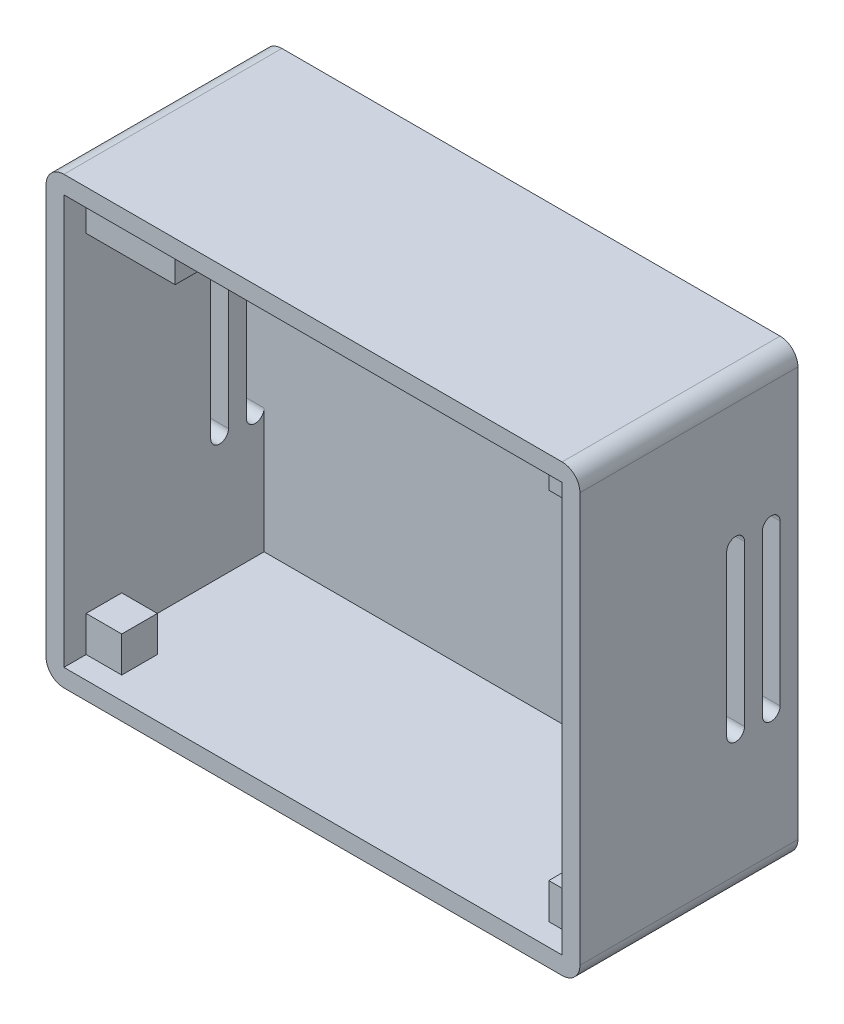
SolidWorks part; units mm, degrees
ref_plane "Спереди" through (0, 0, 0) normal (0, 0, 1) x (1, 0, 0)
ref_plane "Сверху" through (0, 0, 0) normal (0, 1, 0) x (1, 0, 0)
ref_plane "Справа" through (0, 0, 0) normal (1, 0, 0) x (0, 0, -1)
sketch "Эскиз1" plane through (0, 0, 0) normal (0, 0, 1) x (1, 0, 0)
  line L0 (-28, -25) -> (28, -25)
  line L5 (30, -23) -> (30, 23)
  line L8 (-30, 23) -> (-30, -23)
  line L9 (-28, 25) -> (28, 25)
  arc A0 (-28, 25) -> (-30, 23) centre (-28, 23) ccw
  arc A1 (28, 25) -> (30, 23) centre (28, 23) cw
  arc A2 (-30, -23) -> (-28, -25) centre (-28, -23) ccw
  arc A3 (28, -25) -> (30, -23) centre (28, -23) ccw
  point P0 (0, 0)
extrude "Бобышка-Вытянуть8" add sketch "Эскиз1" along normal blind 2 contours L9 A1 L5 A3 L0 A2 L8 A0
sketch "Эскиз6" plane through (0, 0, 2) normal (0, 0, 1) x (1, 0, 0)
  line L0 (-28, 25) -> (28, 25)
  line L1 (30, 23) -> (30, -23)
  line L2 (28, -25) -> (-28, -25)
  line L5 (-28, -23) -> (28, -23)
  line L6 (28, 23) -> (28, -23)
  line L7 (-30, -23) -> (-30, 23)
  line L8 (-18, 23) -> (28, 23)
  line L9 (-18, 23) -> (-18, 18)
  line L10 (-18, 18) -> (-28, 18)
  line L11 (-28, 18) -> (-28, -23)
  arc A0 (-28, 25) -> (-30, 23) centre (-28, 23) ccw
  arc A1 (-28, 25) -> (-30, 23) centre (-28, 23) ccw construction
  arc A2 (-28, -25) -> (-30, -23) centre (-28, -23) cw
  arc A3 (-30, -23) -> (-28, -25) centre (-28, -23) ccw construction
  arc A4 (28, -25) -> (30, -23) centre (28, -23) ccw
  arc A5 (28, -25) -> (30, -23) centre (28, -23) ccw construction
  arc A6 (28, 25) -> (30, 23) centre (28, 23) cw
  arc A7 (30, 23) -> (28, 25) centre (28, 23) ccw construction
extrude "Бобышка-Вытянуть11" add sketch "Эскиз6" along normal blind 20
sketch "Эскиз8" plane through (0, 23, 0) normal (0, -1, 0) x (1, 0, 0)
  line L1 (28, 22) -> (24, 22)
  line L2 (28, 22) -> (28, 18)
  line L3 (28, 18) -> (24, 18)
  line L4 (24, 22) -> (24, 18)
extrude "Бобышка-Вытянуть12" add sketch "Эскиз8" along normal blind 4
sketch "Эскиз9" plane through (0, -23, 0) normal (0, 1, 0) x (1, 0, 0)
  line L1 (28, -22) -> (24, -22)
  line L2 (28, -22) -> (28, -18)
  line L3 (28, -18) -> (24, -18)
  line L4 (24, -22) -> (24, -18)
  line L5 (-28, -22) -> (-24, -22)
  line L6 (-28, -22) -> (-28, -18)
  line L7 (-28, -18) -> (-24, -18)
  line L8 (-24, -22) -> (-24, -18)
extrude "Бобышка-Вытянуть13" add sketch "Эскиз9" along normal blind 4
sketch "Эскиз10" plane through (0, 0, 22) normal (0, 0, 1) x (1, 0, 0)
  line L0 (-28, 25) -> (28, 25)
  line L1 (-30, 23) -> (-30, -23)
  line L2 (-28, -25) -> (28, -25)
  line L3 (30, -23) -> (30, 23)
  line L5 (-28, 23) -> (28, 23)
  line L6 (-28, 23) -> (-28, -23)
  line L7 (-28, -23) -> (28, -23)
  line L8 (28, 23) -> (28, -23)
  arc A0 (-28, 25) -> (-30, 23) centre (-28, 23) ccw
  arc A1 (-28, 25) -> (-30, 23) centre (-28, 23) ccw construction
  arc A2 (-28, -25) -> (-30, -23) centre (-28, -23) cw
  arc A3 (28, -25) -> (30, -23) centre (28, -23) ccw
  arc A4 (28, -25) -> (30, -23) centre (28, -23) ccw construction
  arc A5 (28, 25) -> (30, 23) centre (28, 23) cw
extrude "Бобышка-Вытянуть14" add sketch "Эскиз10" along normal blind 2.5
sketch "Эскиз11" plane through (-30, 0, 0) normal (-1, 0, 0) x (0, 0, 1)
  line L0 (0, 23) -> (24.5, 23)
  point P3 (0, 0)
  point P4 (0, 0)
sketch "Эскиз15" plane through (-30, 0, 0) normal (-1, 0, 0) x (0, 0, 1)
  line L11 (8, 9) -> (8, -9)
  line L16 (6, -9) -> (6, 9)
  line L17 (4, 9) -> (4, -9)
  line L18 (2, -9) -> (2, 9)
  arc A0 (8, -9) -> (6, -9) centre (7, -9) cw
  arc A1 (8, 9) -> (6, 9) centre (7, 9) ccw
  arc A2 (4, 9) -> (2, 9) centre (3, 9) ccw
  arc A3 (4, -9) -> (2, -9) centre (3, -9) cw
extrude "Вырез-Вытянуть5" cut sketch "Эскиз15" against normal blind 60
sketch "0" plane through (-30, 0, 0) normal (-1, 0, 0) x (0, 0, 1)
  line L0 (0, 0) -> (24.5, 0)
  line L1 (0, 23) -> (0, -23) construction
  line L2 (24.5, 23) -> (24.5, -23) construction
  line L3 (12.25, 0) -> (12.25, 5)
  line L4 (12.25, 0) -> (12.25, -5)
  line L5 (12.25, -5) -> (11.75, -5)
  line L6 (12.25, -5) -> (12.75, -5)
  line L7 (12.75, 5) -> (13.75, 5)
  line L8 (12.75, 5) -> (12.75, -5)
  line L9 (13.75, 5) -> (13.75, 4)
  point P13 (0, 0)
